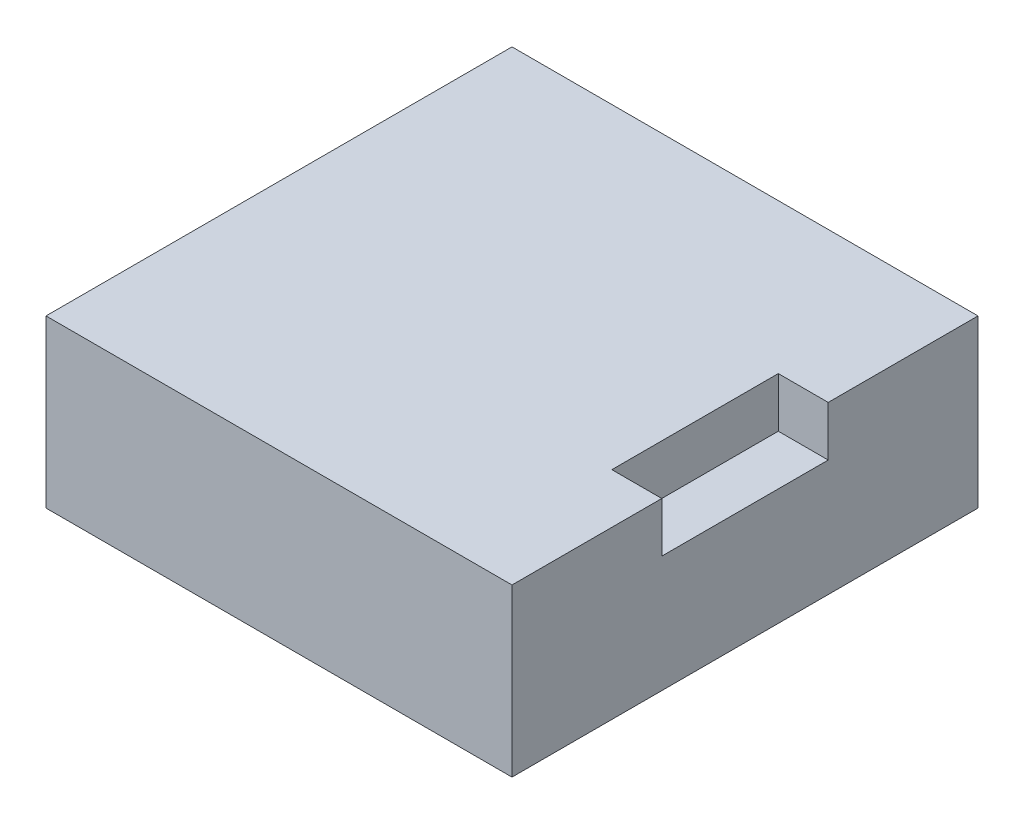
SolidWorks part; units mm, degrees
ref_plane "Front Plane" through (0, 0, 0) normal (0, 0, 1) x (1, 0, 0)
ref_plane "Top Plane" through (0, 0, 0) normal (0, 1, 0) x (1, 0, 0)
ref_plane "Right Plane" through (0, 0, 0) normal (1, 0, 0) x (0, 0, -1)
sketch "Sketch1" plane through (0, 0, 0) normal (0, 1, 0) x (1, 0, 0)
  line L1 (-14, -14) -> (14, -14)
  line L2 (-14, -14) -> (-14, 14)
  line L3 (-14, 14) -> (14, 14)
  line L4 (14, -14) -> (14, 14)
  line L5 (-14, -14) -> (14, 14) construction
  line L6 (-14, 14) -> (14, -14) construction
  point P0 (0, 0)
  dimension "D1" = 28
  dimension "D2" = 28
extrude "Boss-Extrude1" add sketch "Sketch1" along normal mid plane 10 contours L3 L4 L1 L2
sketch "Sketch2" plane through (0, 0, 0) normal (0, 0, 1) x (1, 0, 0)
  line L0 (11, 5) -> (11, 2)
  line L1 (-14, 5) -> (14, 5) construction
  line L2 (11, 2) -> (14, 2)
  line L3 (14, 5) -> (14, -5) construction
  line L4 (14, 2) -> (14, 5)
  line L5 (14, 5) -> (11, 5)
  dimension "D1" = 3
  dimension "D2" = 3
extrude "Cut-Extrude1" cut sketch "Sketch2" against normal mid plane 10
sketch "Sketch3" plane through (0, -5, 0) normal (0, -1, 0) x (1, 0, 0)
  line L0 (0, 0) -> (-14, 0)
  line L1 (-14, 14) -> (-14, -14) construction
sketch "Sketch4" plane through (0, 5, 0) normal (0, 1, 0) x (1, 0, 0)
  line L0 (11, 0) -> (-14, 0)
  line L1 (11, 5) -> (11, -5) construction
  line L2 (-14, -14) -> (-14, 14) construction
